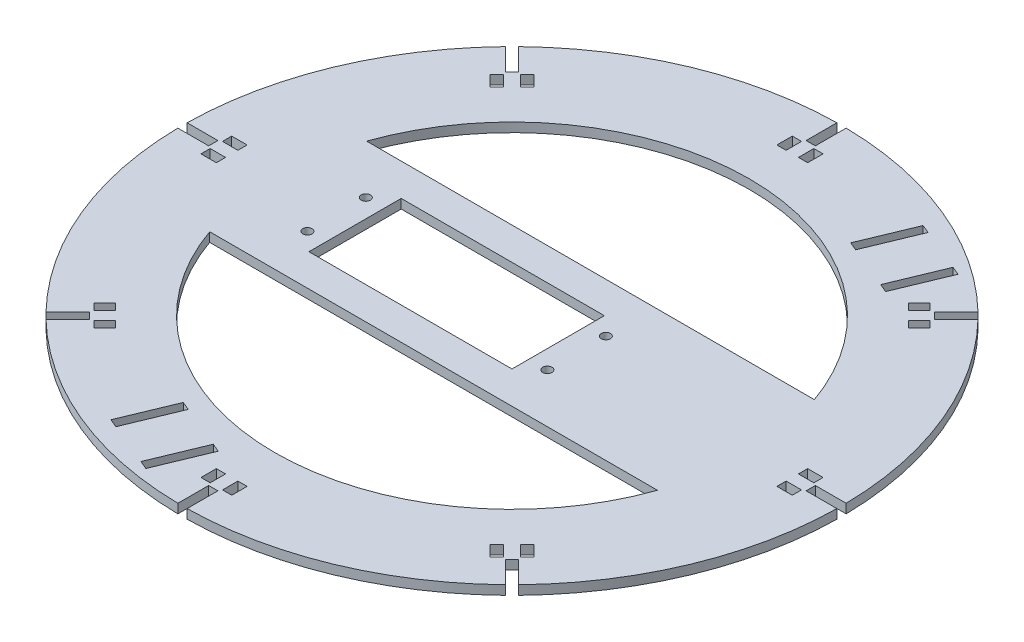
SolidWorks part; units mm, degrees
ref_plane "Front Plane" through (0, 0, 0) normal (0, 0, 1) x (1, 0, 0)
ref_plane "Top Plane" through (0, 0, 0) normal (0, 1, 0) x (1, 0, 0)
ref_plane "Right Plane" through (0, 0, 0) normal (1, 0, 0) x (0, 0, -1)
sketch "Sketch1" plane through (0, 0, 0) normal (0, 1, 0) x (1, 0, 0)
  circle A0 centre (0, 0) radius 107.09
  dimension "D1" = 214.18
extrude "Boss-Extrude1" add sketch "Sketch1" along normal blind 3
sketch "Sketch2" plane through (0, 3, 0) normal (0, 1, 0) x (1, 0, 0)
  line L0 (-1.5, 107.0795) -> (-1.5, 97.0795)
  line L1 (-1.5, 97.0795) -> (1.5, 97.0795)
  line L2 (1.5, 97.0795) -> (1.5, 107.0795)
  line L16 (0, 97.0795) -> (0, 107.09) construction
  circle A0 centre (0, 0) radius 107.09 construction
  dimension "D1" = 10
  dimension "D2" = 10
  dimension "D3" = 3
extrude "Cut-Extrude1" cut sketch "Sketch2" against normal blind 3 and the other way through all
sketch "Sketch3" plane through (0, 3, 0) normal (0, 1, 0) x (1, 0, 0)
  line L0 (0, 0) -> (0, 43.9961) construction
pattern_circular "CirPattern1" count 8 over 360 about axis through (0, 3, 0) along (0, 0, -1) of "Cut-Extrude1"
sketch "Sketch4" plane through (0, 3, 0) normal (0, 1, 0) x (1, 0, 0)
  line L3 (-51, -15) -> (15, -15)
  line L4 (-51, -15) -> (-51, 15)
  line L5 (-51, 15) -> (15, 15)
  line L6 (15, -15) -> (15, 15)
  line L8 (72.7504, -25.5) -> (-72.7504, -25.5)
  line L9 (72.7504, 25.5) -> (-72.7504, 25.5)
  arc A0 (-72.7504, -25.5) -> (72.7504, -25.5) centre (0, 0) ccw
  arc A1 (72.7504, 25.5) -> (-72.7504, 25.5) centre (0, 0) ccw
  circle A2 centre (-57, 9.5) radius 1.5
  circle A3 centre (-57, -9.5) radius 1.5
  circle A4 centre (21, -9.5) radius 1.5
  circle A5 centre (21, 9.5) radius 1.5
  dimension "D1" = 154.18
  dimension "D7" = 3
  dimension "D11" = 6
  dimension "D12" = 6
  dimension "D13" = 3
  dimension "D14" = 5.5
  dimension "D15" = 3
  dimension "D16" = 3
  dimension "D2" = 145.5008
  dimension "D3" = 30
  dimension "D4" = 66
  dimension "D5" = 6
  dimension "D6" = 5.5
  dimension "D8" = 15
  dimension "D9" = 15
  dimension "D10" = 6
  dimension "D17" = 5.5
  dimension "D18" = 5.5
  dimension "D19" = 145.5008
sketch "Sketch7" plane through (0, 3, 0) normal (0, 1, 0) x (1, 0, 0)
  line L0 (-5, 96.0795) -> (-2, 96.0795)
  line L1 (-5, 96.0795) -> (-5, 91.0795)
  line L2 (-5, 91.0795) -> (-2, 91.0795)
  line L3 (-2, 96.0795) -> (-2, 91.0795)
  line L4 (0, 97.0795) -> (0, 116.8402) construction
  line L5 (2, 96.0795) -> (2, 91.0795)
  line L6 (5, 91.0795) -> (2, 91.0795)
  line L7 (5, 96.0795) -> (5, 91.0795)
  line L8 (5, 96.0795) -> (2, 96.0795)
  line L9 (-1.5, 97.0795) -> (1.5, 97.0795) construction
  line L10 (-1.5, 107.0795) -> (-1.5, 97.0795) construction
  dimension "D1" = 3
  dimension "D2" = 5
  dimension "D3" = 0.5
  dimension "D4" = 1
extrude "Cut-Extrude4" cut sketch "Sketch7" against normal blind 3
pattern_circular "CirPattern2" count 8 over 360 about axis through (0, 0, 0) along (0, 1, 0) of "Cut-Extrude4"
extrude "Cut-Extrude5" cut sketch "Sketch4" against normal blind 10
sketch "Sketch9" plane through (0, 3, 0) normal (0, 1, 0) x (1, 0, 0)
  line L0 (-38.078, -91.9284) -> (0, 0) construction
  line L1 (0, 0) -> (37.0002, -15.326) construction
  line L2 (-35.8794, -94.4599) -> (-33.1077, -95.6079)
  line L3 (-35.8794, -94.4599) -> (-28.9911, -77.8301)
  line L4 (-28.9911, -77.8301) -> (-26.2194, -78.9781)
  line L5 (-26.2194, -78.9781) -> (-33.1077, -95.6079)
  line L6 (-19.2496, -101.3482) -> (-16.4779, -102.4962)
  line L7 (-19.2496, -101.3482) -> (-12.3613, -84.7184)
  line L8 (-12.3613, -84.7184) -> (-9.5896, -85.8664)
  line L9 (-9.5896, -85.8664) -> (-16.4779, -102.4962)
  line L10 (53.9358, 67.4976) -> (60.8241, 84.1274)
  line L11 (51.1642, 68.6456) -> (53.9358, 67.4976)
  line L12 (58.0525, 85.2755) -> (51.1642, 68.6456)
  line L13 (58.0525, 85.2755) -> (60.8241, 84.1274)
  line L14 (37.306, 74.3859) -> (44.1943, 91.0157)
  line L15 (34.5344, 75.534) -> (37.306, 74.3859)
  line L16 (41.4227, 92.1638) -> (34.5344, 75.534)
  line L17 (41.4227, 92.1638) -> (44.1943, 91.0157)
  line L18 (-74.656, -76.7773) -> (-1.5, -107.0795) construction
  dimension "D1" = 18
  dimension "D2" = 3
  dimension "D3" = 18
  dimension "D4" = 3
  dimension "D5" = 15
  dimension "D6" = 83
  dimension "D7" = 3
extrude "Cut-Extrude6" cut sketch "Sketch9" against normal blind 3
sketch "Sketch10" plane through (0, 3, 0) normal (0, 1, 0) x (1, 0, 0)
  text T0 "B6" font "Century Gothic" height in points 22
  dimension "D1" = 20
  dimension "D2" = 3
